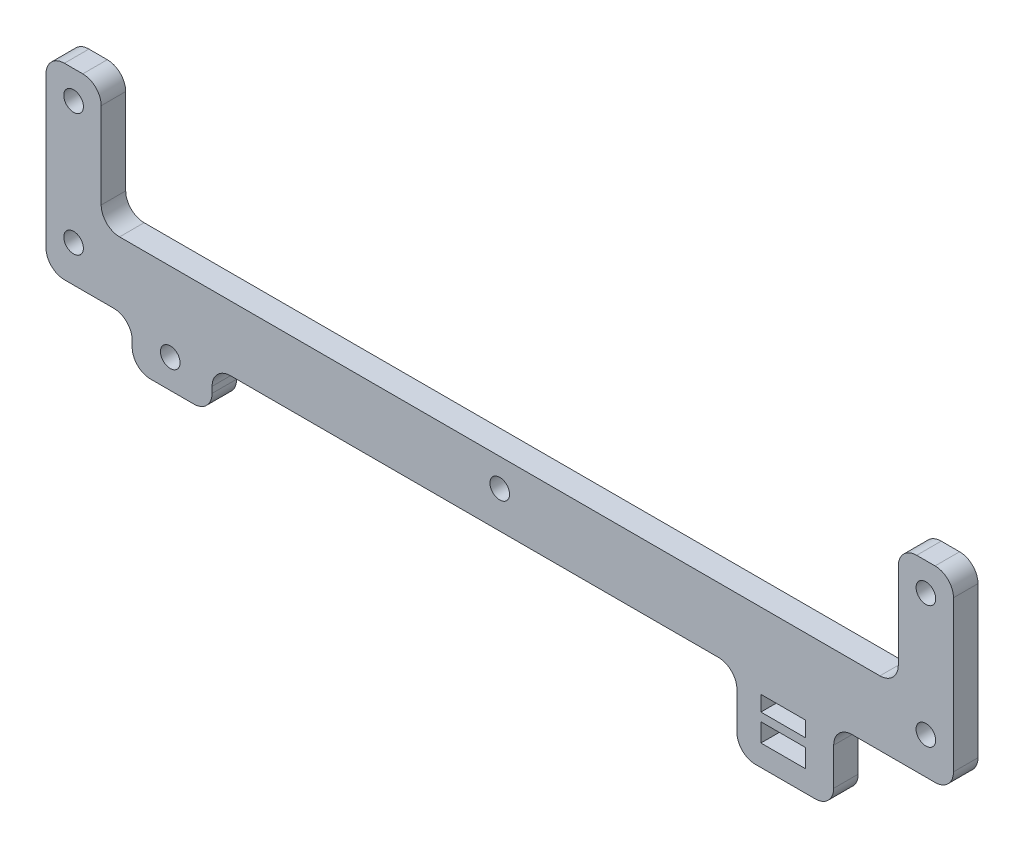
SolidWorks part; units mm, degrees
material "Thornel Mat VMA"
ref_plane "Plano frontal" through (0, 0, 0) normal (0, 0, 1) x (1, 0, 0)
ref_plane "Plano superior" through (0, 0, 0) normal (0, 1, 0) x (1, 0, 0)
ref_plane "Plano direito" through (0, 0, 0) normal (1, 0, 0) x (0, 0, -1)
sketch "Esboço1" plane through (0, 0, 0) normal (0, 0, 1) x (1, 0, 0)
  line L0 (-49.2953, -236.3545) -> (30.2957, -236.3545)
  line L1 (-99.4493, -65.2653) -> (-82.4233, -65.2653)
  line L2 (-99.4493, -65.2653) -> (-99.4493, -233.3545)
  line L4 (84.6139, -65.2653) -> (84.6139, -231.2078)
  line L5 (84.6139, -65.2653) -> (71.6439, -65.2653)
  line L6 (52.0773, -236.3545) -> (68.6439, -236.3545)
  line L8 (71.6439, -47.3545) -> (71.6439, -65.2653)
  line L9 (-79.4233, -44.3545) -> (68.6439, -44.3545)
  line L10 (33.2957, -239.3545) -> (33.2957, -245.448)
  line L11 (71.6439, -231.2078) -> (84.6139, -231.2078)
  line L12 (36.2957, -248.448) -> (46.0773, -248.448)
  line L13 (49.0773, -239.3545) -> (49.0773, -245.448)
  line L14 (-65.3336, -239.3545) -> (-65.3336, -240.3545)
  line L15 (-62.3336, -243.3545) -> (-55.2953, -243.3545)
  line L16 (-52.2953, -239.3545) -> (-52.2953, -240.3545)
  line L33 (-82.4233, -47.3545) -> (-82.4233, -65.2653)
  line L45 (-96.4493, -236.3545) -> (-68.3336, -236.3545)
  line L46 (71.6439, -233.3545) -> (71.6439, -231.2078)
  line L58 (37.2111, -238.1088) -> (37.2111, -240.6088)
  line L59 (44.5163, -240.6088) -> (37.2111, -240.6088)
  line L60 (44.5163, -238.1088) -> (44.5163, -240.6088)
  line L61 (44.5163, -238.1088) -> (37.2111, -238.1088)
  line L62 (44.5163, -244.9817) -> (37.2111, -244.9817)
  line L63 (44.5163, -241.9817) -> (44.5163, -244.9817)
  line L64 (37.2111, -241.9817) -> (44.5163, -241.9817)
  line L65 (37.2111, -244.9817) -> (37.2111, -241.9817)
  line L66 (44.5163, -52.6001) -> (44.5163, -50.1001)
  line L67 (44.5163, -52.6001) -> (37.2111, -52.6001)
  line L68 (44.5163, -50.1001) -> (37.2111, -50.1001)
  line L69 (44.5163, -48.7273) -> (37.2111, -48.7273)
  line L70 (37.2111, -52.6001) -> (37.2111, -50.1001)
  line L71 (44.5163, -45.7273) -> (44.5163, -48.7273)
  line L72 (44.5163, -45.7273) -> (37.2111, -45.7273)
  line L73 (37.2111, -45.7273) -> (37.2111, -48.7273)
  arc A0 (49.0773, -239.3545) -> (52.0773, -236.3545) centre (52.0773, -239.3545) cw
  arc A1 (71.6439, -47.3545) -> (68.6439, -44.3545) centre (68.6439, -47.3545) ccw
  arc A2 (46.0773, -248.448) -> (49.0773, -245.448) centre (46.0773, -245.448) ccw
  arc A3 (33.2957, -245.448) -> (36.2957, -248.448) centre (36.2957, -245.448) ccw
  arc A4 (33.2957, -239.3545) -> (30.2957, -236.3545) centre (30.2957, -239.3545) ccw
  arc A5 (-55.2953, -243.3545) -> (-52.2953, -240.3545) centre (-55.2953, -240.3545) ccw
  arc A6 (-65.3336, -240.3545) -> (-62.3336, -243.3545) centre (-62.3336, -240.3545) ccw
  arc A7 (-49.2953, -236.3545) -> (-52.2953, -239.3545) centre (-49.2953, -239.3545) ccw
  arc A8 (-68.3336, -236.3545) -> (-65.3336, -239.3545) centre (-68.3336, -239.3545) cw
  arc A9 (-99.4493, -233.3545) -> (-96.4493, -236.3545) centre (-96.4493, -233.3545) ccw
  arc A24 (-79.4233, -44.3545) -> (-82.4233, -47.3545) centre (-79.4233, -47.3545) ccw
  arc A37 (68.6439, -236.3545) -> (71.6439, -233.3545) centre (68.6439, -233.3545) ccw
  point P19 (49.0773, -236.3545)
  point P37 (-65.3336, -243.3545)
  point P50 (-65.3336, -236.3545)
  dimension "D1" = 3
  dimension "D3" = 3
  dimension "D4" = 3
  dimension "D5" = 3
  dimension "D2" = 7
extrude "Ressalto-extrusão1" add sketch "Esboço1" along normal blind 4
sketch "Sketch1" plane through (0, 0, 4) normal (0, 0, 1) x (1, 0, 0)
  line L0 (-79.3861, -236.3545) -> (-79.3861, -228.7929)
  line L1 (-96.4493, -236.3545) -> (-68.3336, -236.3545) construction
  line L2 (-70.3861, -225.7929) -> (59.6139, -225.7929)
  line L3 (68.6139, -228.7929) -> (68.6139, -236.3545)
  line L4 (52.0773, -236.3545) -> (68.6439, -236.3545) construction
  line L6 (-79.3861, -205.766) -> (-70.3861, -205.766)
  line L7 (-79.3861, -205.766) -> (-79.3861, -228.7929)
  line L8 (68.6139, -205.766) -> (59.6139, -205.766)
  line L9 (-70.3861, -205.766) -> (-70.3861, -225.7929)
  line L10 (68.6139, -205.766) -> (68.6139, -228.7929)
  line L12 (59.6139, -205.766) -> (59.6139, -225.7929)
  line L23 (-82.4233, -47.3545) -> (-82.4233, -65.2653)
  line L24 (-82.4233, -65.2653) -> (-99.4493, -65.2653)
  line L25 (-99.4493, -65.2653) -> (-99.4493, -233.3545)
  line L26 (-96.4493, -236.3545) -> (-68.3336, -236.3545)
  line L27 (-65.3336, -239.3545) -> (-65.3336, -240.3545)
  line L28 (-62.3336, -243.3545) -> (-55.2953, -243.3545)
  line L29 (-52.2953, -240.3545) -> (-52.2953, -239.3545)
  line L30 (-49.2953, -236.3545) -> (30.2957, -236.3545)
  line L31 (33.2957, -239.3545) -> (33.2957, -245.448)
  line L32 (36.2957, -248.448) -> (46.0773, -248.448)
  line L33 (49.0773, -245.448) -> (49.0773, -239.3545)
  line L34 (52.0773, -236.3545) -> (68.6439, -236.3545)
  line L35 (71.6439, -233.3545) -> (71.6439, -231.2078)
  line L36 (71.6439, -231.2078) -> (84.6139, -231.2078)
  line L37 (84.6139, -231.2078) -> (84.6139, -65.2653)
  line L38 (84.6139, -65.2653) -> (71.6439, -65.2653)
  line L39 (71.6439, -65.2653) -> (71.6439, -47.3545)
  line L40 (68.6439, -44.3545) -> (-79.4233, -44.3545)
  line L41 (-82.4233, -47.3545) -> (-82.4233, -65.2653)
  line L42 (-82.4233, -65.2653) -> (-99.4493, -65.2653)
  line L43 (-99.4493, -65.2653) -> (-99.4493, -233.3545)
  line L44 (-96.4493, -236.3545) -> (-79.3861, -236.3545)
  line L52 (68.6139, -236.3545) -> (68.6439, -236.3545)
  line L53 (71.6439, -233.3545) -> (71.6439, -231.2078)
  line L54 (71.6439, -231.2078) -> (84.6139, -231.2078)
  line L55 (84.6139, -231.2078) -> (84.6139, -65.2653)
  line L56 (84.6139, -65.2653) -> (71.6439, -65.2653)
  line L57 (71.6439, -65.2653) -> (71.6439, -47.3545)
  line L58 (68.6439, -44.3545) -> (-79.4233, -44.3545)
  arc A22 (-99.4493, -233.3545) -> (-96.4493, -236.3545) centre (-96.4493, -233.3545) ccw
  arc A23 (-65.3336, -239.3545) -> (-68.3336, -236.3545) centre (-68.3336, -239.3545) ccw
  arc A24 (-65.3336, -240.3545) -> (-62.3336, -243.3545) centre (-62.3336, -240.3545) ccw
  arc A25 (-55.2953, -243.3545) -> (-52.2953, -240.3545) centre (-55.2953, -240.3545) ccw
  arc A26 (-49.2953, -236.3545) -> (-52.2953, -239.3545) centre (-49.2953, -239.3545) ccw
  arc A27 (33.2957, -239.3545) -> (30.2957, -236.3545) centre (30.2957, -239.3545) ccw
  arc A28 (33.2957, -245.448) -> (36.2957, -248.448) centre (36.2957, -245.448) ccw
  arc A29 (46.0773, -248.448) -> (49.0773, -245.448) centre (46.0773, -245.448) ccw
  arc A30 (52.0773, -236.3545) -> (49.0773, -239.3545) centre (52.0773, -239.3545) ccw
  arc A31 (68.6439, -236.3545) -> (71.6439, -233.3545) centre (68.6439, -233.3545) ccw
  arc A36 (71.6439, -47.3545) -> (68.6439, -44.3545) centre (68.6439, -47.3545) ccw
  arc A37 (-79.4233, -44.3545) -> (-82.4233, -47.3545) centre (-79.4233, -47.3545) ccw
  arc A40 (-99.4493, -233.3545) -> (-96.4493, -236.3545) centre (-96.4493, -233.3545) ccw
  arc A49 (68.6439, -236.3545) -> (71.6439, -233.3545) centre (68.6439, -233.3545) ccw
  arc A54 (71.6439, -47.3545) -> (68.6439, -44.3545) centre (68.6439, -47.3545) ccw
  arc A55 (-79.4233, -44.3545) -> (-82.4233, -47.3545) centre (-79.4233, -47.3545) ccw
  dimension "D2" = 0
extrude "Cut-Extrude1" cut sketch "Sketch1" against normal blind 10
hole_wizard "Furo com folga de M31" positions "Esboço3" profile "Esboço2" hole size "M3" standard "ISO" end condition through all
sketch "Esboço3" plane through (0, 0, 4) normal (0, 0, 1) x (1, 0, 0)
  line L1 (-74.8861, -50.3545) -> (64.1139, -50.3545)
  line L2 (-74.8861, -50.3545) -> (-74.8861, -230.3545)
  line L3 (-74.8861, -230.3545) -> (64.1139, -230.3545)
  line L4 (64.1139, -50.3545) -> (64.1139, -230.3545)
  line L9 (-74.8861, -140.3545) -> (64.1139, -140.3545) construction
  line L17 (-5.3861, -50.3545) -> (-5.3861, -230.3545) construction
  point P0 (-74.8861, -50.3545)
  point P2 (64.1139, -230.3545)
  point P4 (64.1139, -50.3545)
  point P6 (-74.8861, -230.3545)
  point P213 (-59.1219, -47.4775)
  point P217 (-5.3861, -50.3545)
  point P218 (-59.1219, -238.6514)
  point P222 (-5.3861, -230.3545)
  point P223 (64.1139, -210.3545)
  point P225 (-74.8861, -210.3545)
  dimension "D1" = 69.5
sketch "Esboço2" plane through (-74.8861, -50.3545, 4) normal (1, 0, 0) x (0, -1, 0)
  line L0 (0, 0) -> (0, 4)
  line L1 (0, 4) -> (1.6, 4)
  line L2 (1.6, 4) -> (1.6, 0)
  line L5 (1.6, 0) -> (0, 0)
  line L11 (0, -6.35) -> (0, 107.95) construction
  dimension "Thru Hole Dia." = 3.2
  dimension "Thru Hole Depth" = 4
fillet "Fillet1" radius 3 8 edges at (-79.3861, -236.3545, 2) (68.6139, -236.3545, 2) (-70.3861, -225.7929, 2) (-70.3861, -205.766, 2) (-79.3861, -205.766, 2) (59.6139, -225.7929, 2) (59.6139, -205.766, 2) (68.6139, -205.766, 2)
